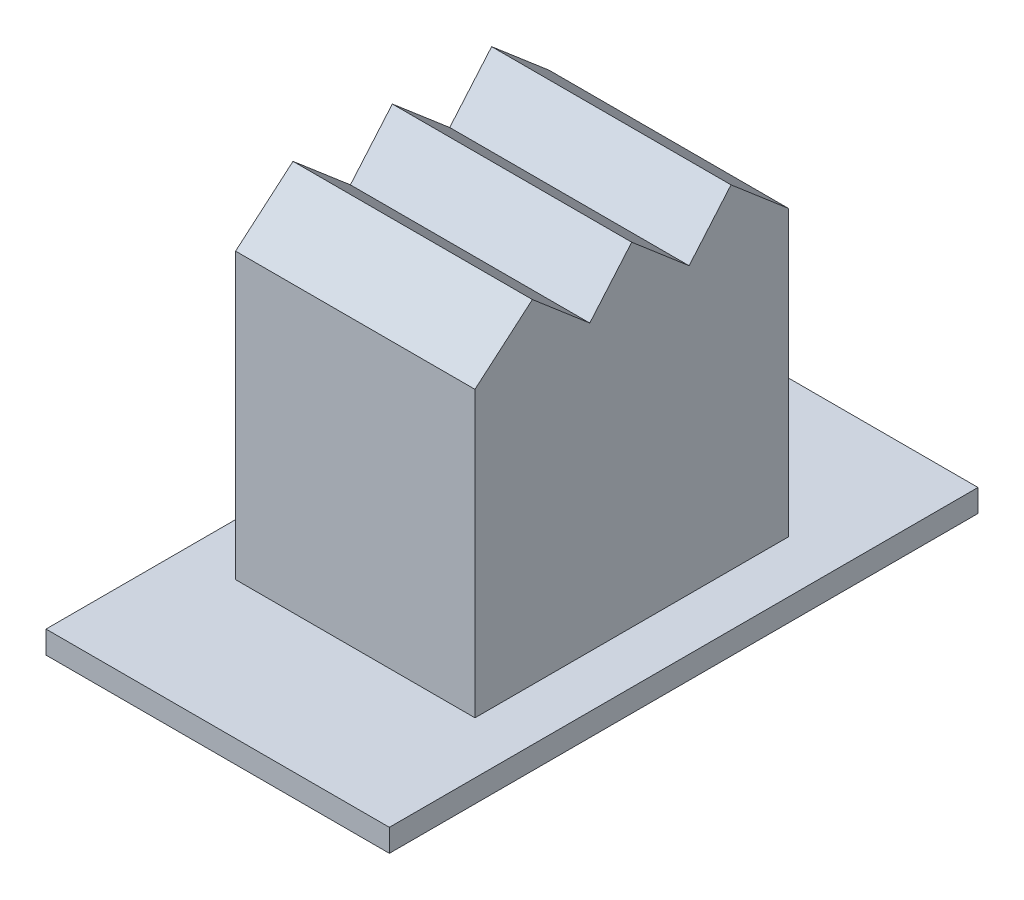
SolidWorks part; units mm, degrees
ref_plane "Přední rovina" through (0, 0, 0) normal (0, 0, 1) x (1, 0, 0)
ref_plane "Horní rovina" through (0, 0, 0) normal (0, 1, 0) x (1, 0, 0)
ref_plane "Pravá rovina" through (0, 0, 0) normal (1, 0, 0) x (0, 0, -1)
sketch "Skica1" plane through (0, 0, 0) normal (0, 1, 0) x (1, 0, 0)
  line L1 (0, 0) -> (7, 0)
  line L2 (0, 0) -> (0, 12)
  line L3 (0, 12) -> (7, 12)
  line L4 (7, 0) -> (7, 12)
  line L5 (2.27, 4.815) -> (4.73, 4.815)
  line L6 (2.27, 4.815) -> (2.27, 7.185)
  line L7 (2.27, 7.185) -> (4.73, 7.185)
  line L8 (4.73, 4.815) -> (4.73, 7.185)
  point P9 (3.5, 4.815)
  point P10 (3.5, 0)
  point P11 (4.73, 6)
  point P12 (7, 6)
  dimension "D1" = 7
  dimension "D2" = 12
  dimension "D3" = 2.46
  dimension "D4" = 2.37
extrude "Přidat vysunutím1" add sketch "Skica1" along normal blind 0.46
sketch "Skica2" plane through (0, 0.46, 0) normal (0, 1, 0) x (1, 0, 0)
  line L5 (1.06, 2.805) -> (5.94, 2.805)
  line L6 (1.06, 2.805) -> (1.06, 9.195)
  line L7 (1.06, 9.195) -> (5.94, 9.195)
  line L8 (5.94, 2.805) -> (5.94, 9.195)
  line L9 (2.27, 7.185) -> (4.73, 7.185)
  line L10 (2.27, 7.185) -> (2.27, 4.815)
  line L11 (2.27, 4.815) -> (4.73, 4.815)
  line L12 (4.73, 7.185) -> (4.73, 4.815)
  dimension "D1" = 1.21
  dimension "D2" = 1.21
  dimension "D3" = 2.01
  dimension "D4" = 2.01
extrude "Přidat vysunutím2" add sketch "Skica2" along normal blind 4
sketch "Skica3" plane through (0, 4.46, 0) normal (0, 1, 0) x (1, 0, 0)
  line L1 (1.06, 2.805) -> (5.94, 2.805)
  line L2 (1.06, 2.805) -> (1.06, 9.195)
  line L3 (1.06, 9.195) -> (5.94, 9.195)
  line L4 (5.94, 2.805) -> (5.94, 9.195)
extrude "Přidat vysunutím3" add sketch "Skica3" along normal blind 2.8
sketch "Skica4" plane through (1.06, 0, 0) normal (-1, 0, 0) x (0, 0, 1)
  line L0 (-9.195, 6.26) -> (-2.805, 6.26) construction
  line L1 (-9.195, 7.26) -> (-9.195, 0.46) construction
  line L2 (-2.805, 7.26) -> (-2.805, 0.46) construction
  line L3 (-9.195, 7.26) -> (-2.805, 7.26) construction
  line L4 (-9.195, 6.26) -> (-8.0248, 7.26)
  line L5 (-8.0248, 7.26) -> (-7.1702, 6.26)
  line L6 (-7.1702, 6.26) -> (-6, 7.26)
  line L7 (-6, 7.26) -> (-5.1455, 6.26)
  line L8 (-5.1455, 6.26) -> (-3.9752, 7.26)
  line L9 (-3.9752, 7.26) -> (-2.805, 6.26)
  line L10 (-9.195, 6.26) -> (-9.195, 7.26)
  line L11 (-9.195, 7.26) -> (-2.805, 7.26)
  line L12 (-2.805, 7.26) -> (-2.805, 6.26)
  line M5 (-2.805, 0.46) -> (-2.805, 7.26)
  line M6 (-2.805, 7.26) -> (-9.195, 7.26)
  line M7 (-9.195, 7.26) -> (-9.195, 0.46)
  dimension "D1" = 1
extrude "Odebrat vysunutím1" cut sketch "Skica4" against normal blind 10 contours L4 M7 M6 | L5 L6 M6 | L7 L8 M6 | L9 M6 M5
